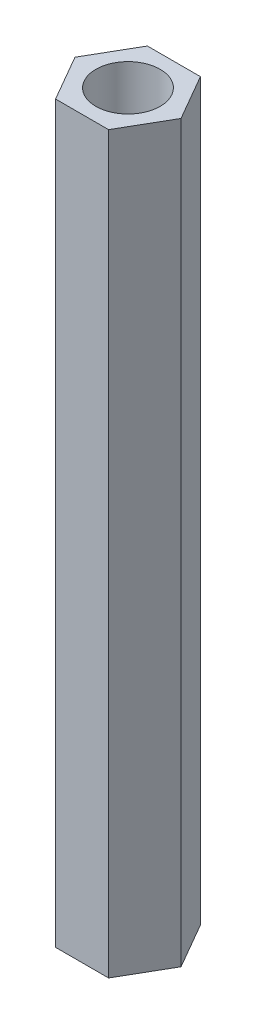
SolidWorks part; units mm, degrees
ref_plane "Front" through (0, 0, 0) normal (0, 0, 1) x (1, 0, 0)
ref_plane "Top" through (0, 0, 0) normal (0, 1, 0) x (1, 0, 0)
ref_plane "Right" through (0, 0, 0) normal (1, 0, 0) x (0, 0, -1)
sketch "草圖1" plane through (0, 0, 0) normal (0, 1, 0) x (1, 0, 0)
  line L0 (-5.8913, 0) -> (5.8913, 0) construction
  line L1 (2.8868, 0) -> (1.4434, 2.5)
  line L2 (1.4434, 2.5) -> (-1.4434, 2.5)
  line L3 (-1.4434, 2.5) -> (-2.8868, 0)
  line L4 (-2.8868, 0) -> (-1.4434, -2.5)
  line L5 (-1.4434, -2.5) -> (1.4434, -2.5)
  line L6 (1.4434, -2.5) -> (2.8868, 0)
  circle A0 centre (0, 0) radius 2.5 construction
  circle A1 centre (0, 0) radius 1.75
  point P12 (0, 0)
  dimension "D2" = 3.5
  dimension "D1" = 5
extrude "填料-伸長1" add sketch "草圖1" along normal blind 40
